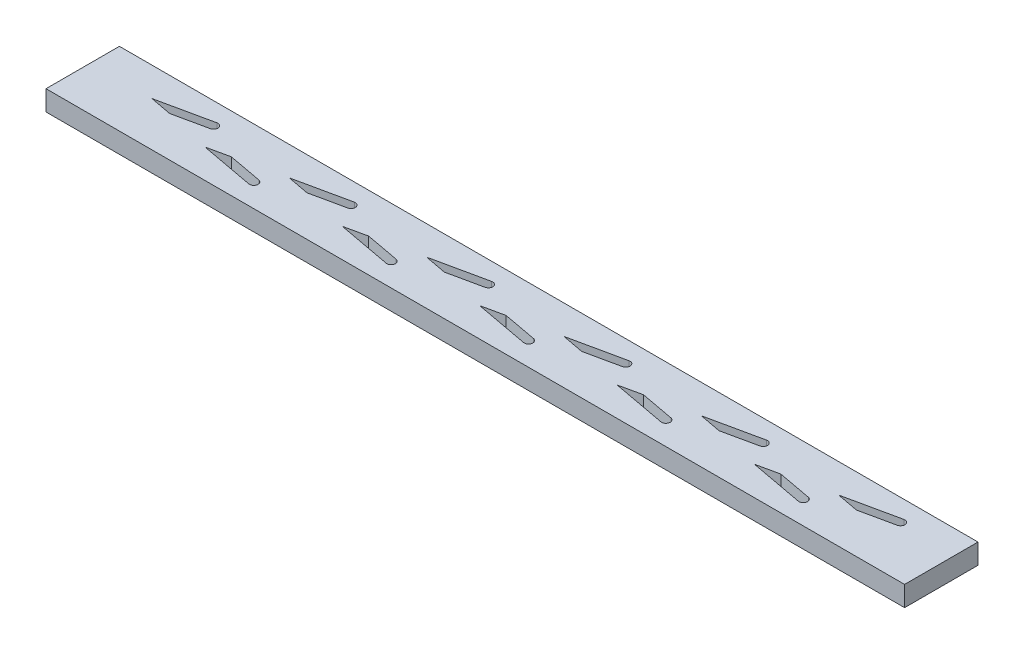
SolidWorks part; units mm, degrees
ref_plane "Front Plane" through (0, 0, 0) normal (0, 0, 1) x (1, 0, 0)
ref_plane "Top Plane" through (0, 0, 0) normal (0, 1, 0) x (1, 0, 0)
ref_plane "Right Plane" through (0, 0, 0) normal (1, 0, 0) x (0, 0, -1)
sketch "Sketch1" plane through (0, 0, 0) normal (0, 1, 0) x (1, 0, 0)
  line L1 (0, 0) -> (200, 0)
  line L2 (0, 0) -> (0, 17.1)
  line L3 (0, 17.1) -> (200, 17.1)
  line L4 (200, 0) -> (200, 17.1)
  dimension "D1" = 17.1
  dimension "D2" = 200
extrude "Boss-Extrude1" add sketch "Sketch1" along normal blind 4.7
sketch "Sketch2" plane through (0, 4.7, 0) normal (0, 1, 0) x (1, 0, 0)
  line L0 (0, 8.55) -> (200, 8.55) construction
  line L1 (0, 17.1) -> (0, 0) construction
  line L2 (200, 0) -> (200, 17.1) construction
  line L4 (0, 12.05) -> (200, 12.05) construction
  line L5 (27, 17.1) -> (27, 0) construction
  line L6 (200, 17.1) -> (0, 17.1) construction
  line L7 (0, 0) -> (200, 0) construction
  line L18 (26.79, 13.0277) -> (14.3243, 10.35)
  line L19 (14.3243, 10.35) -> (19.3884, 9.3922)
  line L20 (19.3884, 9.3922) -> (27.21, 11.0723)
  arc A0 (26.79, 13.0277) -> (27.21, 11.0723) centre (27, 12.05) cw
  dimension "D5" = 1
  dimension "D2" = 27
  dimension "D4" = 3.5
  dimension "D6" = 12.75
  dimension "D7" = 8
  dimension "D8" = 1.8
extrude "Cut-Extrude1" cut sketch "Sketch2" against normal up to next (4.7 mm away)
pattern_linear "LPattern1" count 6 spacing 32 along (1, 0, 0) of "Cut-Extrude1"
sketch "Sketch3" plane through (0, 4.7, 0) normal (0, 1, 0) x (1, 0, 0)
  line L0 (0, 8.55) -> (200, 8.55) construction
  line L1 (0, 17.1) -> (0, 0) construction
  line L2 (200, 0) -> (200, 17.1) construction
  line L3 (0, 5.4) -> (200, 5.4) construction
  line L4 (43, 17.1) -> (43, 0) construction
  line L5 (200, 17.1) -> (0, 17.1) construction
  line L6 (0, 0) -> (200, 0) construction
  line L7 (42.817, 4.4169) -> (30.2823, 6.75)
  line L8 (43.183, 6.3831) -> (35.3181, 7.847)
  line L9 (30.2823, 6.75) -> (35.3181, 7.847)
  arc A1 (43.183, 6.3831) -> (42.817, 4.4169) centre (43, 5.4) cw
  dimension "D3" = 1
  dimension "D1" = 3.15
  dimension "D2" = 43
  dimension "D4" = 1.8
  dimension "D6" = 12.75
  dimension "D7" = 8
extrude "Cut-Extrude2" cut sketch "Sketch3" against normal up to next (4.7 mm away)
pattern_linear "LPattern2" count 5 spacing 32 along (1, 0, 0) of "Cut-Extrude2"
